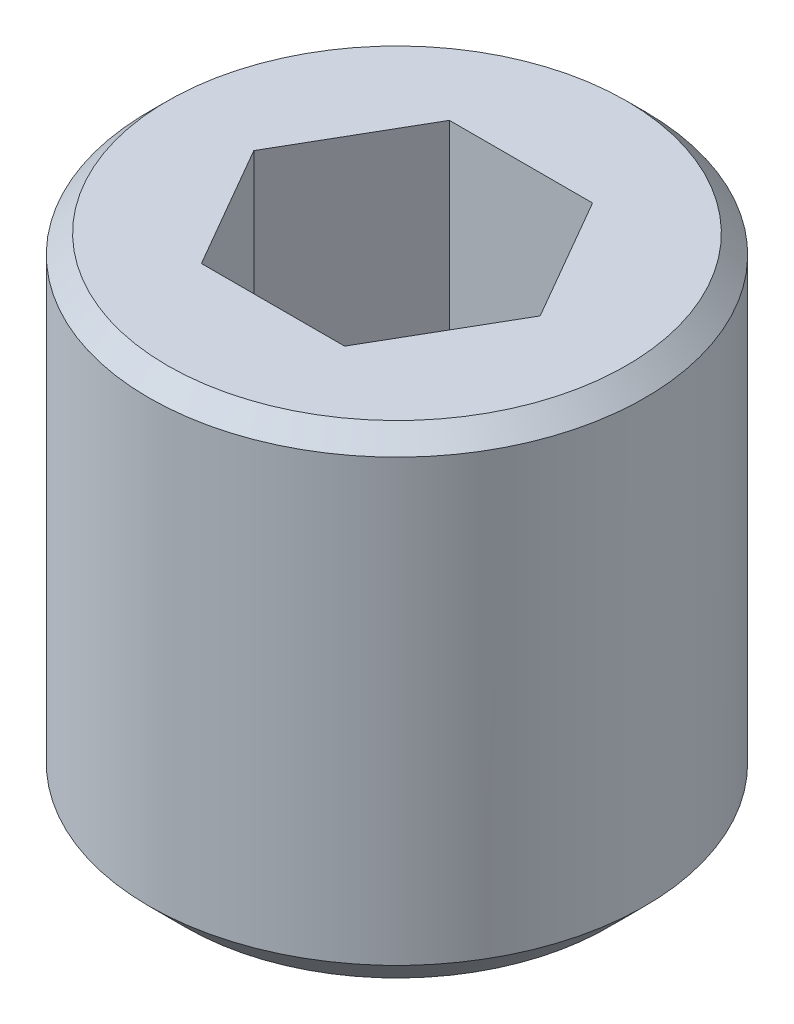
SolidWorks part; units mm, degrees
material "acero"
ref_plane "Alzado" through (0, 0, 0) normal (0, 0, 1) x (1, 0, 0)
ref_plane "Planta" through (0, 0, 0) normal (0, 1, 0) x (1, 0, 0)
ref_plane "Vista lateral" through (0, 0, 0) normal (1, 0, 0) x (0, 0, -1)
sketch "Croquis1" plane through (0, 0, 0) normal (0, 0, 1) x (1, 0, 0)
  line L0 (0, 0) -> (0, -60.9498) construction
  line L1 (0, 0) -> (2, 0)
  line L4 (2, 0) -> (2, -4)
  line L5 (2, -4) -> (0, -4)
  line L6 (0, -4) -> (0, 0)
  dimension "D1" = 4
  dimension "D4" = 4
revolve "Revolución1" add sketch "Croquis1" angle 360 about L0
cosmetic thread "Rosca cosmética1" parameters "D2"=3.22
sketch "Croquis3" plane through (0, 0, 0) normal (0, 1, 0) x (1, 0, 0)
  line L1 (-0.5774, 1) -> (-1.1547, 0)
  line L2 (-1.1547, 0) -> (-0.5774, -1)
  line L3 (-0.5774, -1) -> (0.5774, -1)
  line L4 (0.5774, -1) -> (1.1547, 0)
  line L5 (1.1547, 0) -> (0.5774, 1)
  line L6 (0.5774, 1) -> (-0.5774, 1)
  circle A0 centre (0, 0) radius 1 construction
  dimension "D1" = 2
extrude "Cortar-Extruir2" cut sketch "Croquis3" against normal blind 2
chamfer "Chaflán3" distance 0.3 angle 45 1 edges at (0, -4, 2)
chamfer "Chaflán4" distance 0.15 angle 45 1 edges at (0, 0, 2)
